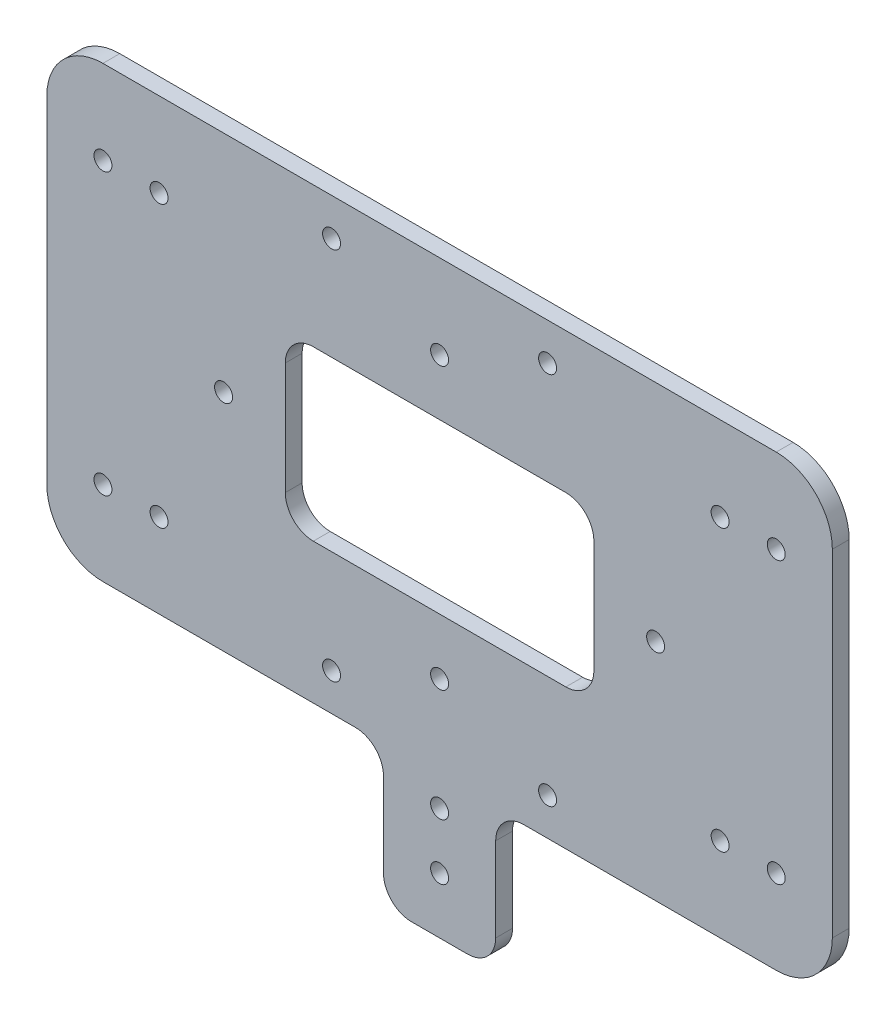
SolidWorks part; units mm, degrees
material "A-玻璃纤维"
ref_plane "前视基准面" through (0, 0, 0) normal (0, 0, 1) x (1, 0, 0)
ref_plane "上视基准面" through (0, 0, 0) normal (0, 1, 0) x (1, 0, 0)
ref_plane "右视基准面" through (0, 0, 0) normal (1, 0, 0) x (0, 0, -1)
sketch "草图1" plane through (0, 0, 0) normal (0, 0, 1) x (1, 0, 0)
  line L0 (0, 101.7727) -> (0, -94.6691) construction
  line L1 (-208.4633, 0) -> (191.5239, 0) construction
  line L2 (0, 0) -> (26.9668, 46.7078) construction
  line L3 (-70, -40) -> (70, -40)
  line L4 (-70, -40) -> (-70, 40)
  line L5 (-70, 40) -> (70, 40)
  line L6 (70, -40) -> (70, 40)
  line L7 (-70, -40) -> (70, 40) construction
  line L8 (-70, 40) -> (70, -40) construction
  circle A0 centre (19.25, 33.342) radius 1.6
  circle A1 centre (38.5, 0) radius 1.6
  circle A2 centre (19.25, -33.342) radius 1.6
  circle A3 centre (-19.25, -33.342) radius 1.6
  circle A4 centre (-38.5, 0) radius 1.6
  circle A5 centre (-19.25, 33.342) radius 1.6
  point P5 (0, 0)
  point P26 (0, 0)
  dimension "D2" = 38.5
  dimension "D3" = 3.2
  dimension "D1" = 60
  dimension "D5" = 80
  dimension "D6" = 140
  dimension "D4" = 6
extrude "凸台-拉伸1" add sketch "草图1" along normal blind 3
sketch "草图2" plane through (0, 0, 3) normal (0, 0, 1) x (1, 0, 0)
  line L0 (-90.4043, 0) -> (107.1806, 0) construction
  line L1 (0, 81.7389) -> (0, -80.791) construction
  line L2 (-71.0178, 25) -> (71.0957, 25) construction
  circle A0 centre (0, 25) radius 1.6
  circle A1 centre (-60, 25) radius 1.6
  circle A2 centre (60, 25) radius 1.6
  circle A3 centre (60, -25) radius 1.6
  circle A4 centre (-60, -25) radius 1.6
  circle A5 centre (0, -25) radius 1.6
  dimension "D1" = 3.2
  dimension "D2" = 50
  dimension "D3" = 60
extrude "切除-拉伸1" cut sketch "草图2" against normal blind 10
sketch "草图3" plane through (0, 0, 3) normal (0, 0, 1) x (1, 0, 0)
  line L0 (0, 85.1834) -> (0, -82.3194) construction
  line L1 (137.2979, 0) -> (-136.129, 0) construction
  line L3 (-27.5, -15) -> (27.5, -15)
  line L4 (-27.5, -15) -> (-27.5, 15)
  line L5 (-27.5, 15) -> (27.5, 15)
  line L6 (27.5, -15) -> (27.5, 15)
  line L7 (-27.5, -15) -> (27.5, 15) construction
  line L8 (-27.5, 15) -> (27.5, -15) construction
  point P5 (0, 0)
  dimension "D1" = 55
  dimension "D2" = 30
extrude "切除-拉伸2" cut sketch "草图3" against normal blind 10
fillet "圆角1" radius 5 4 edges at (27.5, -15, 1.5) (27.5, 15, 1.5) (-27.5, -15, 1.5) (-27.5, 15, 1.5)
fillet "圆角2" radius 10 4 edges at (-70, -40, 1.5) (70, -40, 1.5) (70, 40, 1.5) (-70, 40, 1.5)
sketch "草图4" plane through (0, 0, 3) normal (0, 0, 1) x (1, 0, 0)
  line L0 (0, 59.4893) -> (0, -40) construction
  line L1 (-60, -40) -> (60, -40) construction
  line L2 (115.1191, 0) -> (-125.2044, 0) construction
  circle A0 centre (-50, 25) radius 1.6
  circle A1 centre (-60, 25) radius 1.6 construction
  circle A2 centre (-50, -25) radius 1.6
  circle A3 centre (50, -25) radius 1.6
  circle A4 centre (50, 25) radius 1.6
  dimension "D1" = 25
  dimension "D2" = 10
extrude "切除-拉伸3" cut sketch "草图4" against normal blind 10
sketch "草图6" plane through (0, 0, 3) normal (0, 0, 1) x (1, 0, 0)
  line L0 (0, 83.4201) -> (0, -133.4416) construction
  line L1 (-10, -40) -> (-10, -65)
  line L2 (-60, -40) -> (60, -40) construction
  line L3 (-10, -65) -> (10, -65)
  line L4 (10, -65) -> (10, -40)
  line L5 (10, -40) -> (-10, -40)
  dimension "D1" = 20
  dimension "D2" = 25
extrude "凸台-拉伸2" add sketch "草图6" against normal blind 3
sketch "草图7" plane through (0, 0, 3) normal (0, 0, 1) x (1, 0, 0)
  line L1 (-10, -40) -> (-10, -65) construction
  circle A0 centre (0, -45) radius 1.6
  circle A1 centre (0, -55) radius 1.6
  circle A2 centre (50, -25) radius 1.6 construction
  dimension "D1" = 20
  dimension "D2" = 10
  dimension "D3" = 3.2
  dimension "D4" = 10
extrude "切除-拉伸5" cut sketch "草图7" against normal through all
fillet "圆角3" radius 5 4 edges at (10, -40, 1.5) (10, -65, 1.5) (-10, -65, 1.5) (-10, -40, 1.5)
